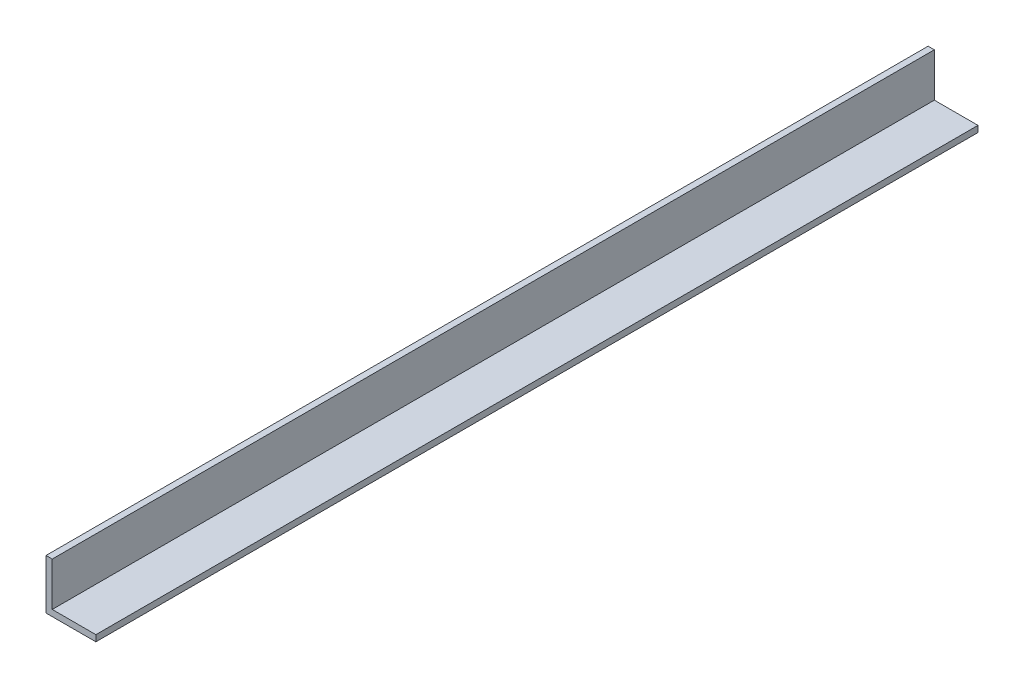
SolidWorks part; units mm, degrees
ref_plane "Front Plane" through (0, 0, 0) normal (0, 0, 1) x (1, 0, 0)
ref_plane "Top Plane" through (0, 0, 0) normal (0, 1, 0) x (1, 0, 0)
ref_plane "Right Plane" through (0, 0, 0) normal (1, 0, 0) x (0, 0, -1)
sketch "Sketch1" plane through (0, 0, 0) normal (0, 0, 1) x (1, 0, 0)
  line L0 (0, 25.4) -> (0, 0)
  line L1 (0, 0) -> (25.4, 0)
  line L2 (25.4, 0) -> (25.4, 3.175)
  line L3 (25.4, 3.175) -> (3.175, 3.175)
  line L4 (3.175, 3.175) -> (3.175, 25.4)
  line L5 (3.175, 25.4) -> (0, 25.4)
  dimension "D1" = 25.4
  dimension "D2" = 3.175
extrude "Boss-Extrude1" add sketch "Sketch1" along normal mid plane 449.2
